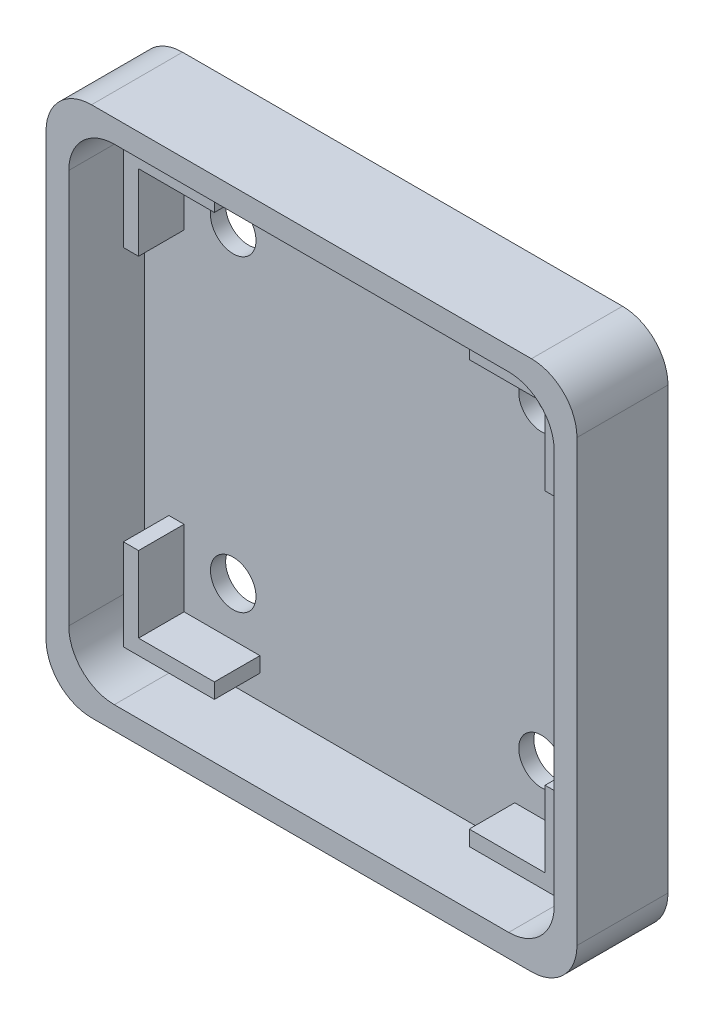
SolidWorks part; units mm, degrees
ref_plane "Front Plane" through (0, 0, 0) normal (0, 0, 1) x (1, 0, 0)
ref_plane "Top Plane" through (0, 0, 0) normal (0, 1, 0) x (1, 0, 0)
ref_plane "Right Plane" through (0, 0, 0) normal (1, 0, 0) x (0, 0, -1)
sketch "Sketch1" plane through (0, 0, 0) normal (0, 0, 1) x (1, 0, 0)
  line L1 (3, 0) -> (32, 0)
  line L2 (0, -3) -> (0, -32)
  line L3 (3, -35) -> (32, -35)
  line L4 (35, -3) -> (35, -32)
  arc A0 (3, -35) -> (0, -32) centre (3, -32) cw
  arc A1 (35, -3) -> (32, 0) centre (32, -3) ccw
  arc A2 (3, 0) -> (0, -3) centre (3, -3) ccw
  arc A3 (32, -35) -> (35, -32) centre (32, -32) ccw
  point P9 (35, 0)
  point P12 (0, 0)
  point P15 (35, -35)
  dimension "D3" = 3
  dimension "D1" = 35
  dimension "D2" = 35
extrude "Boss-Extrude1" add sketch "Sketch1" along normal blind 10
sketch "Sketch2" plane through (0, 0, 10) normal (0, 0, 1) x (1, 0, 0)
  line L0 (0, 0) -> (1.5, 0) construction
  line L1 (32, 0) -> (3, 0) construction
  line L2 (1.5, 0) -> (1.5, -1.5) construction
  line L3 (1.5, -4.5) -> (1.5, -30.5)
  line L5 (4.5, -33.5) -> (30.5, -33.5)
  line L6 (33.5, -30.5) -> (33.5, -4.5)
  line L7 (30.5, -1.5) -> (4.5, -1.5)
  arc A0 (33.5, -4.5) -> (30.5, -1.5) centre (30.5, -4.5) ccw
  arc A1 (4.5, -1.5) -> (1.5, -4.5) centre (4.5, -4.5) ccw
  arc A2 (1.5, -30.5) -> (4.5, -33.5) centre (4.5, -30.5) ccw
  arc A3 (30.5, -33.5) -> (33.5, -30.5) centre (30.5, -30.5) ccw
  point P16 (1.5, -33.5)
  point P19 (33.5, -33.5)
  dimension "D5" = 3
  dimension "D1" = 1.5
  dimension "D2" = 1.5
  dimension "D3" = 32
  dimension "D4" = 32
extrude "Cut-Extrude1" cut sketch "Sketch2" against normal blind 9
sketch "Sketch3" plane through (0, 0, 1) normal (0, 0, 1) x (1, 0, 0)
  line L0 (32, 0) -> (3, 0) construction
  line L1 (0, 0) -> (35, -35) construction
  line L2 (4.1, -4.1) -> (9.1, -4.1)
  line L3 (4.1, -4.1) -> (9.1, -4.1)
  line L4 (4.1, -4.1) -> (4.1, -9.1)
  line L7 (0, -35) -> (35, 0) construction
  line L8 (17.5, 0) -> (17.5, -35) construction
  line L9 (9.1, -4.1) -> (9.1, -3.1)
  line L10 (9.1, -3.1) -> (3.1, -3.1)
  line L11 (3.1, -3.1) -> (3.1, -9.1)
  line L12 (3.1, -9.1) -> (4.1, -9.1)
  line L13 (0, -17.5) -> (35, -17.5) construction
  line L14 (0, -3) -> (0, -32) construction
  line L15 (35, -32) -> (35, -3) construction
  line L34 (3, -35) -> (32, -35) construction
  line L35 (30.9, -4.1) -> (30.9, -9.1)
  line L36 (30.9, -9.1) -> (31.9, -9.1)
  line L37 (31.9, -3.1) -> (25.9, -3.1)
  line L38 (30.9, -4.1) -> (25.9, -4.1)
  line L39 (25.9, -3.1) -> (25.9, -4.1)
  line L40 (31.9, -9.1) -> (31.9, -3.1)
  line L41 (30.9, -30.9) -> (25.9, -30.9)
  line L42 (25.9, -30.9) -> (25.9, -31.9)
  line L43 (31.9, -31.9) -> (31.9, -25.9)
  line L44 (30.9, -30.9) -> (30.9, -25.9)
  line L45 (31.9, -25.9) -> (30.9, -25.9)
  line L46 (25.9, -31.9) -> (31.9, -31.9)
  line L47 (4.1, -30.9) -> (4.1, -25.9)
  line L48 (4.1, -25.9) -> (3.1, -25.9)
  line L49 (3.1, -31.9) -> (9.1, -31.9)
  line L50 (4.1, -30.9) -> (9.1, -30.9)
  line L51 (9.1, -31.9) -> (9.1, -30.9)
  line L52 (3.1, -25.9) -> (3.1, -31.9)
  point P8 (17.2452, -17.2452)
  point P44 (17.5, -7.34)
  point P45 (17.5, -17.5)
  point P54 (17.5, -17.5)
  dimension "D1" = 4
  dimension "D3" = 1
  dimension "D4" = 1
  dimension "D5" = 6
  dimension "D6" = 6
sketch "Sketch5" plane through (0, 0, 1) normal (0, 0, 1) x (1, 0, 0)
  line L0 (0, -35) -> (35, 0) construction
  line L1 (35, -35) -> (0, 0) construction
  line L2 (17.5, -17.5) -> (17.5, -7.34) construction
  line L3 (7.34, -7.34) -> (27.66, -7.34) construction
  circle A0 centre (7.34, -7.34) radius 1.5
  circle A1 centre (27.66, -7.34) radius 1.5
  circle A2 centre (27.66, -27.66) radius 1.5
  circle A3 centre (7.34, -27.66) radius 1.5
  point P12 (17.5, -7.34)
  point P23 (17.5, -17.5)
  dimension "D2" = 4
  dimension "D1" = 10.16
extrude "Cut-Extrude2" cut sketch "Sketch5" against normal through all contours A0 | A3 | A2 | A1
extrude "Boss-Extrude2" add sketch "Sketch3" along normal blind 3 contours L11 L12 L4 L2 L9 L10 | L36 L40 L37 L39 L38 L35 | L42 L46 L43 L45 L44 L41 | L52 L49 L51 L50 L47 L48
sketch "Sketch7" plane through (0, 0, 10) normal (0, 0, 1) x (1, 0, 0)
  circle A0 centre (16.499, -17.5) radius 24.9102
extrude "Cut-Extrude5" cut sketch "Sketch7" against normal blind 4
